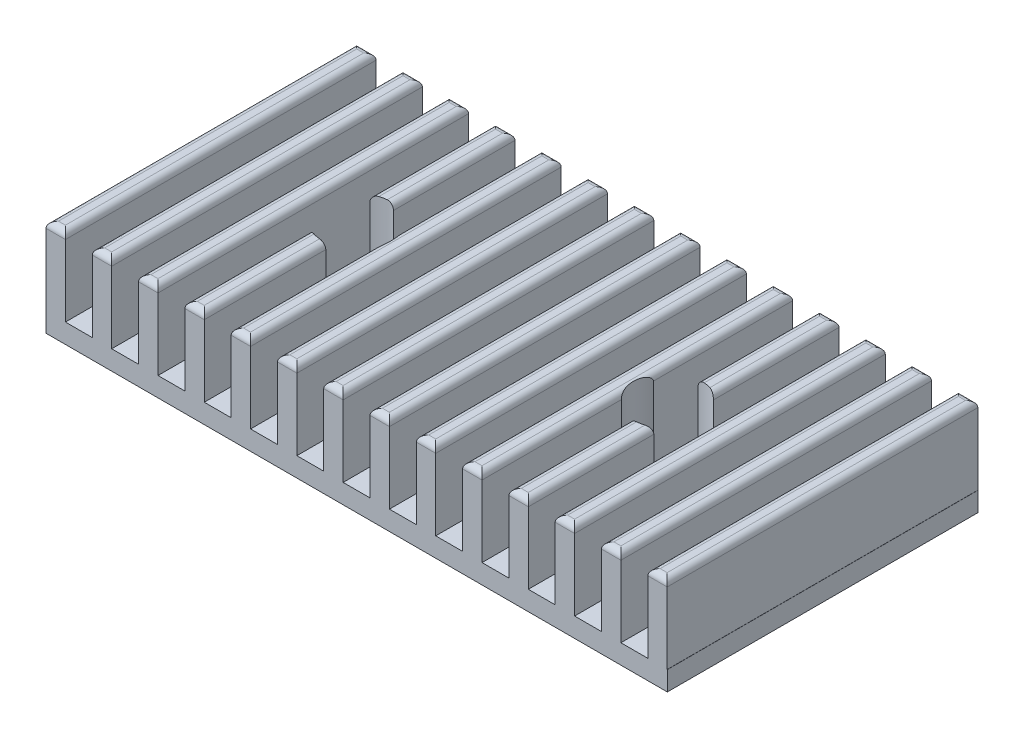
SolidWorks part; units mm, degrees
material "6061 Alloy"
ref_plane "Front Plane" through (0, 0, 0) normal (0, 0, 1) x (1, 0, 0)
ref_plane "Top Plane" through (0, 0, 0) normal (0, 1, 0) x (1, 0, 0)
ref_plane "Right Plane" through (0, 0, 0) normal (1, 0, 0) x (0, 0, -1)
sketch "Sketch2" plane through (0, 0, 0) normal (0, 1, 0) x (1, 0, 0)
  line L1 (-21.2876, 10.7475) -> (29.5124, 10.7475)
  line L2 (-21.2876, 10.7475) -> (-21.2876, -14.6525)
  line L3 (-21.2876, -14.6525) -> (29.5124, -14.6525)
  line L4 (29.5124, 10.7475) -> (29.5124, -14.6525)
  dimension "D1" = 50.8
  dimension "D2" = 25.4
extrude "Boss-Extrude1" add sketch "Sketch2" along normal blind 1.5875
sketch "Sketch3" plane through (0, 1.5875, 0) normal (0, 1, 0) x (1, 0, 0)
  line L0 (-21.2876, -14.6525) -> (29.5124, -14.6525) construction
  line L1 (-21.2876, 10.7475) -> (-19.7001, 10.7475)
  line L2 (-21.2876, 10.7475) -> (-21.2876, -14.6525)
  line L3 (-21.2876, -14.6525) -> (-19.7001, -14.6525)
  line L4 (-19.7001, 10.7475) -> (-19.7001, -14.6525)
  dimension "D1" = 1.5875
extrude "Boss-Extrude2" add sketch "Sketch3" along normal blind 6.35
fillet "Fillet1" radius 0.508 4 edges at (-20.4939, 7.9375, -10.7475) (-21.2876, 7.9375, 1.9525) (-20.4939, 7.9375, 14.6525) (-19.7001, 7.9375, 1.9525)
pattern_linear "LPattern1" count 14 spacing 3.7846 along (1, 0, 0) of "Boss-Extrude2", "Fillet1"
hole_wizard "CBORE for #4 Socket Head Cap Screw1" positions "3DSketch1" profile "Sketch6" counterbore size "#4" standard "ANSI Inch" end condition through all
sketch3d "3DSketch1"
  line L7 (-21.2876, 7.4295, 14.6525) -> (-21.2876, 7.4295, -10.7475) construction
  line L8 (29.4997, 7.4295, -10.7475) -> (29.4997, 7.4295, 14.6525) construction
  point P22 (-8.5978, 7.9375, 1.9525)
  point P24 (16.8098, 7.9375, 1.9525)
  dimension "D1" = 12.7
  dimension "D2" = 12.7
  dimension "D3" = 12.7
  dimension "D4" = 12.7
sketch "Sketch6" plane through (-8.5978, 7.9375, 1.9525) normal (1, 0, 0) x (0, 0, 1)
  line L0 (0, 0) -> (0, 7.9375)
  line L1 (0, 7.9375) -> (1.6319, 7.9375)
  line L3 (1.6319, 7.9375) -> (1.6319, 6.35)
  line L4 (1.6319, 6.35) -> (2.7788, 6.35)
  line L5 (2.7788, 6.35) -> (2.7788, 0)
  line L7 (2.7788, 0) -> (0, 0)
  line L11 (0, -6.35) -> (0, 107.95) construction
  dimension "Thru Hole Dia." = 3.2639
  dimension "Thru Hole Depth" = 7.9375
  dimension "C'Bore Dia." = 5.5575
  dimension "C'Bore Depth" = 6.35
